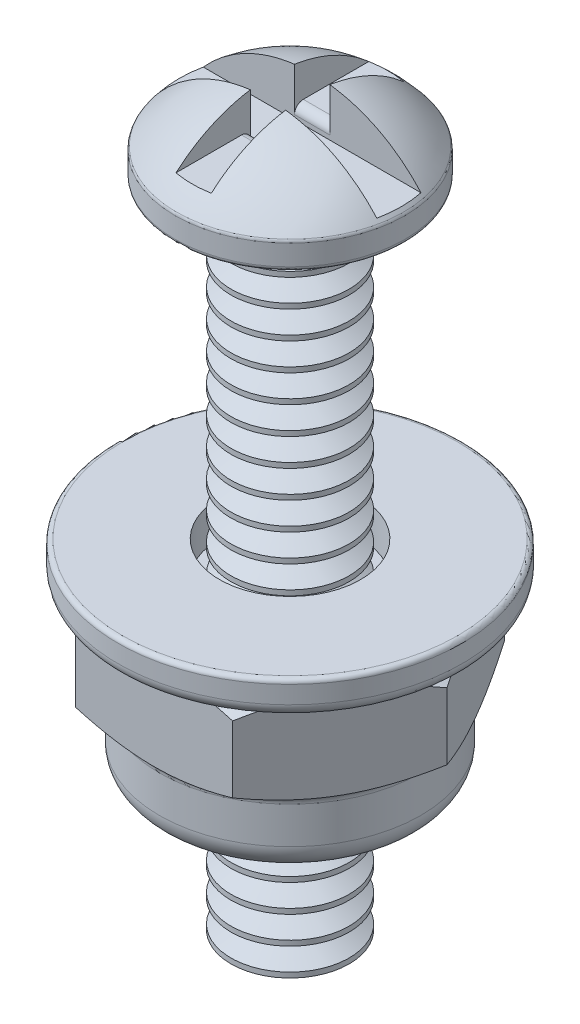
SolidWorks part; units mm, degrees
other "Nut"
other "Screw Body"
other "Washer"
material "Plain Carbon Steel"
ref_plane "Front Plane" through (0, 0, 0) normal (0, 0, 1) x (1, 0, 0)
ref_plane "Top Plane" through (0, 0, 0) normal (0, 1, 0) x (1, 0, 0)
ref_plane "Right Plane" through (0, 0, 0) normal (1, 0, 0) x (0, 0, -1)
sketch "Sketch1" plane through (0, 0, 0) normal (0, 0, 1) x (1, 0, 0)
  line L0 (0, 2.3495) -> (0, -19.05)
  line L1 (0, 0) -> (1.7018, 0) construction
  line L2 (1.7018, 0) -> (3.175, 0)
  line L3 (1.7018, 0) -> (1.7018, -19.05)
  line L4 (1.7018, -19.05) -> (0, -19.05)
  line L5 (3.302, 0.127) -> (3.302, 0.7171)
  line L6 (3.302, 0.762) -> (3.302, 2.3495) construction
  line L7 (3.302, 2.3495) -> (0, 2.3495) construction
  arc A0 (0, 2.3495) -> (3.2733, 0.7975) centre (0, -1.8783) cw
  arc A1 (3.302, 0.7171) -> (3.2733, 0.7975) centre (3.175, 0.7171) ccw
  arc A2 (3.175, 0) -> (3.302, 0.127) centre (3.175, 0.127) ccw
  point P15 (3.302, 0)
  dimension "D5" = 0.127
  dimension "D6" = 3.302
  dimension "D1" = 1.7018
  dimension "D2" = 2.3495
  dimension "D3" = 19.05
  dimension "D4" = 0.762
revolve "Revolve Screw Body" add sketch "Sketch1" angle 360 about L0
sketch "Sketch2" plane through (0, 0, 0) normal (1, 0, 0) x (0, 0, -1)
  line L0 (0, 0) -> (0, 0.889) construction
  line L2 (-0.635, 2.667) -> (0.635, 2.667)
  line L3 (-0.635, 2.667) -> (-0.635, 0.889)
  line L4 (-0.635, 0.889) -> (0.635, 0.889)
  line L5 (0.635, 2.667) -> (0.635, 0.889)
  dimension "D1" = 0.889
  dimension "D2" = 1.27
  dimension "D3" = 1.778
extrude "Long Cut Phillips" cut sketch "Sketch2" against normal through all both and the other way through all
sketch "Sketch3" plane through (0, 0, 0) normal (0, 0, 1) x (1, 0, 0)
  line L0 (0, 0) -> (0, 1.27) construction
  line L2 (-0.508, 2.54) -> (0.508, 2.54)
  line L3 (-0.508, 2.54) -> (-0.508, 1.27)
  line L4 (-0.508, 1.27) -> (0.508, 1.27)
  line L5 (0.508, 2.54) -> (0.508, 1.27)
  dimension "D1" = 1.016
  dimension "D2" = 1.27
  dimension "D3" = 1.27
extrude "Short Cut Phillips" cut sketch "Sketch3" against normal through all both and the other way through all
fillet "Phillips Fillet" radius 0.254 2 edges at (0, 1.27, 0.635) (0, 1.27, -0.635)
sketch "Sketch4" plane through (0, 0, 0) normal (0, 0, 1) x (1, 0, 0)
  line L0 (0, -19.05) -> (0, 0) construction
  line L1 (-1.7018, -19.05) -> (1.7018, -19.05) construction
  line L2 (0, -19.05) -> (1.143, -19.05) construction
  line L3 (1.143, -19.05) -> (1.8304, -19.05) construction
  line L4 (1.8304, -19.05) -> (2.6242, -19.05) construction
  line L5 (2.6242, -18.6531) -> (2.6242, -19.4469)
  line L6 (1.8304, -18.6531) -> (1.8304, -19.4469) construction
  line L7 (2.6242, -18.6531) -> (1.8304, -18.6531)
  line L8 (1.8304, -18.6531) -> (1.143, -19.05)
  line L9 (1.143, -19.05) -> (1.8304, -19.4469)
  line L10 (1.8304, -19.4469) -> (2.6242, -19.4469)
  dimension "D1" = 0.7937
  dimension "D2" = 60
  dimension "D3" = 1.143
revolve "Cut Threading" cut sketch "Sketch4" angle 360 about L0
pattern_linear "LPattern Threads" count 24 spacing 0.7937 along (0, 1, 0) of "Cut Threading"
ref_plane "Plane Nut to Head Gap" through (0, -10, 0) normal (0, -1, 0) x (-1, 0, 0)
sketch "Sketch5" plane through (0, -10, 0) normal (0, -1, 0) x (-1, 0, 0)
  line L1 (-4.5167, 0) -> (-2.2584, -3.9116)
  line L2 (-2.2584, -3.9116) -> (2.2584, -3.9116)
  line L3 (2.2584, -3.9116) -> (4.5167, 0)
  line L4 (4.5167, 0) -> (2.2584, 3.9116)
  line L5 (2.2584, 3.9116) -> (-2.2584, 3.9116)
  line L6 (-2.2584, 3.9116) -> (-4.5167, 0)
  circle A0 centre (0, 0) radius 3.9116 construction
  circle A1 centre (0, 0) radius 1.3525
  dimension "D1" = 7.8232
  dimension "D2" = 2.7051
extrude "Nut Tap Hole #36 Drill 0.1065" add sketch "Sketch5" along normal blind 2.794 separate body
sketch "Sketch6" plane through (0, 0, 0) normal (0, 0, 1) x (1, 0, 0)
  line L0 (0, -10) -> (0, -12.794) construction
  line L1 (2.2584, -10) -> (-2.2584, -10) construction
  line L2 (2.2584, -12.794) -> (-2.2584, -12.794) construction
  line L3 (0, -12.794) -> (3.7592, -12.794) construction
  line L4 (4.5167, -12.794) -> (2.2584, -12.794) construction
  line L5 (3.7592, -12.794) -> (3.7592, -10) construction
  line L6 (4.5167, -10) -> (2.2584, -10) construction
  line L7 (3.7592, -10) -> (0, -10) construction
  line L8 (3.7592, -10) -> (4.5167, -10)
  line L9 (4.5167, -10) -> (4.5167, -10.4374)
  line L10 (4.5167, -12.794) -> (4.5167, -10) construction
  line L11 (4.5167, -10.4374) -> (3.7592, -10)
  line L12 (3.7592, -12.794) -> (4.5167, -12.794)
  line L13 (4.5167, -12.794) -> (4.5167, -12.3566)
  line L14 (4.5167, -12.3566) -> (3.7592, -12.794)
  dimension "D1" = 30
  dimension "D2" = 3.7592
revolve "Nut Angle Edges" cut sketch "Sketch6" angle 360 about L0
sketch "Sketch8" plane through (0, -12.794, 0) normal (0, -1, 0) x (1, 0, 0)
  circle A0 centre (0, 0) radius 1.3525 construction
  circle A1 centre (0, 0) radius 1.3525
  circle A2 centre (0, 0) radius 3.7592 construction
  circle A3 centre (0, 0) radius 3.7592
extrude "Lock Nut Extrude" add sketch "Sketch8" along normal offset from surface (1.9685 mm away) 4.7625 up to face at (-3.7592, -10, 0)
sketch "Sketch9" plane through (0, -14.7625, 0) normal (0, -1, 0) x (1, 0, 0)
  circle A0 centre (0, 0) radius 1.778
  dimension "D1" = 3.556
extrude "Lock Nut Cut" cut sketch "Sketch9" against normal blind 0.508
fillet "Lock Nut Fillet-1" radius 0.762 1 edges at (0, -14.7625, -3.7592)
fillet "Lock Nut Fillet-2" radius 0.254 2 edges at (0, -14.7625, -1.778) (0, -12.794, -3.7592)
sketch "Sketch7" plane through (0, -10, 0) normal (0, -1, 0) x (1, 0, 0)
  circle A0 centre (0, 0) radius 4.953
  circle A1 centre (0, 0) radius 2.032
  dimension "D1" = 4.064
  dimension "D2" = 9.906
extrude "Washer" add sketch "Sketch7" against normal blind 1.016 separate body
fillet "Washer Fillet-1" radius 0.381 1 edges at (0, -10, -4.953)
fillet "Washer Fillet-2" radius 0.127 1 edges at (0, -8.984, -4.953)
